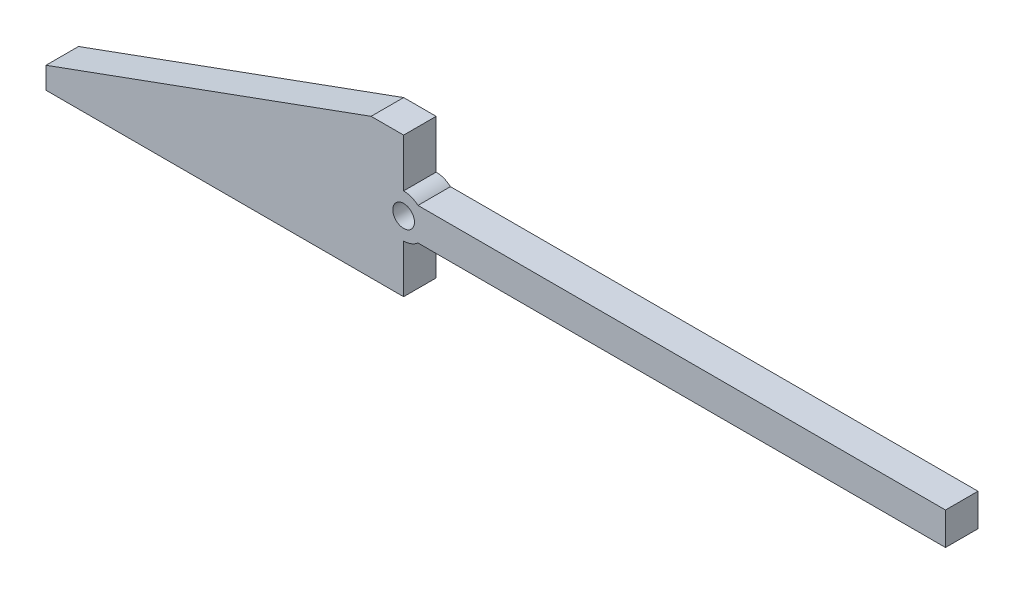
SolidWorks part; units mm, degrees
ref_plane "Спереди" through (0, 0, 0) normal (0, 0, 1) x (1, 0, 0)
ref_plane "Сверху" through (0, 0, 0) normal (0, 1, 0) x (1, 0, 0)
ref_plane "Справа" through (0, 0, 0) normal (1, 0, 0) x (0, 0, -1)
other "Configuration Table"
sketch "Эскиз1" plane through (0, 0, 0) normal (0, 0, 1) x (1, 0, 0)
  line L0 (0, 0) -> (0, 2)
  line L1 (0, 2) -> (30, 12.9191)
  line L11 (33, 12.9191) -> (30, 12.9191)
  line L12 (0, 0) -> (33, 0)
  line L15 (33, 12.9191) -> (33, 8.4596)
  line L16 (34.3229, 7.9596) -> (83, 7.9596)
  line L17 (83, 7.9596) -> (83, 4.9596)
  line L18 (83, 4.9596) -> (34.3229, 4.9596)
  line L19 (33, 4.4596) -> (33, 0)
  line L20 (33, 8.4596) -> (33, 6.4596) construction
  line L21 (33, 6.4596) -> (33, 4.4596) construction
  circle A0 centre (33, 6.4596) radius 1
  arc A1 (33, 4.4596) -> (34.3229, 4.9596) centre (33, 6.4596) ccw
  arc A2 (34.3229, 7.9596) -> (33, 8.4596) centre (33, 6.4596) ccw
  dimension "D7" = 4
  dimension "D8" = 2
  dimension "D1" = 30
  dimension "D2" = 2
  dimension "D3" = 3
  dimension "D4" = 20
  dimension "D5" = 3
  dimension "D6" = 50
extrude "Бобышка-Вытянуть1" add sketch "Эскиз1" along normal blind 3
